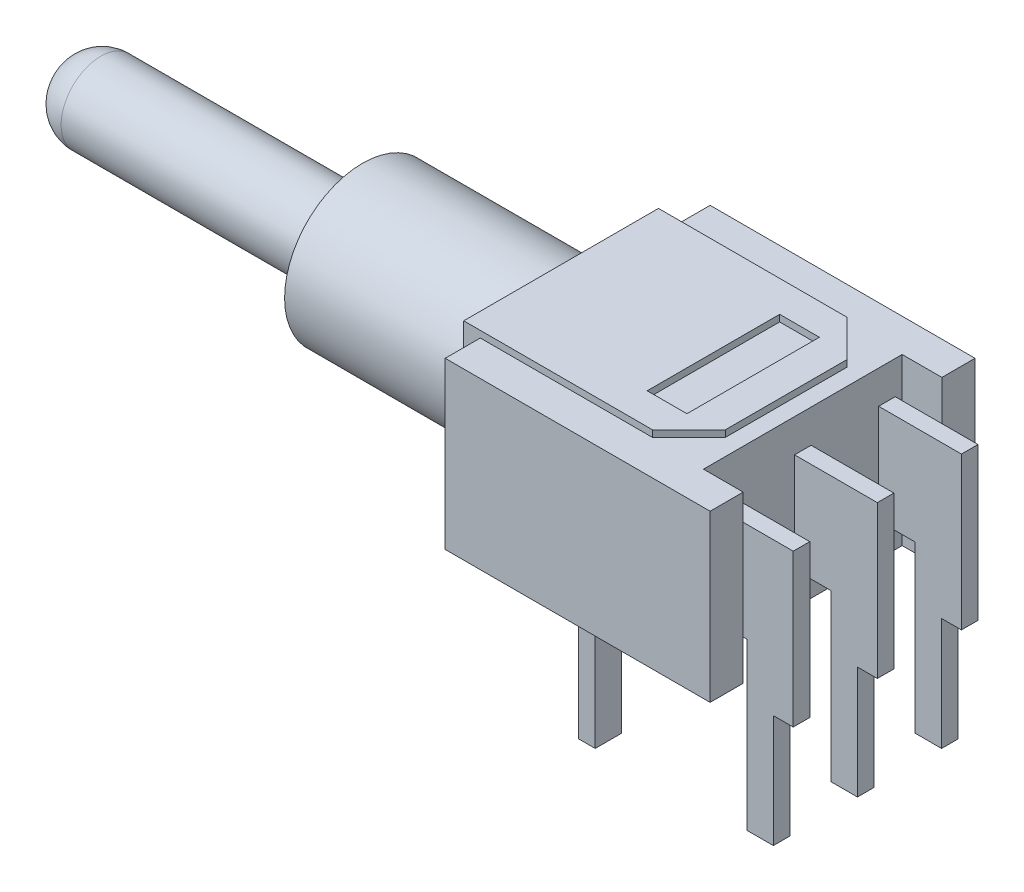
SolidWorks part; units mm, degrees
ref_plane "Plan de face" through (0, 0, 0) normal (0, 0, 1) x (1, 0, 0)
ref_plane "Plan de dessus" through (0, 0, 0) normal (0, 1, 0) x (1, 0, 0)
ref_plane "Plan de droite" through (0, 0, 0) normal (1, 0, 0) x (0, 0, -1)
sketch "Esquisse1" plane through (0, 0, 0) normal (0, 1, 0) x (1, 0, 0)
  line L0 (-0.5576, 4) -> (9.3741, 4) construction
  line L1 (0, 0) -> (8, 0)
  line L2 (0, 0) -> (0, 8)
  line L3 (0, 8) -> (8, 8)
  line L4 (8, 0) -> (8, 1)
  line L5 (9.3741, 7) -> (5.0476, 7) construction
  line L6 (6.8, -1.0514) -> (6.8, 8.7051) construction
  line L7 (8, 7) -> (6.8, 7)
  line L8 (8, 1) -> (6.8, 1)
  line L9 (6.8, 7) -> (6.8, 1)
  line L10 (8, 7) -> (8, 8)
  dimension "D1" = 4
  dimension "D2" = 1.2
  dimension "D3" = 1
extrude "Boss.-Extru.1" add sketch "Esquisse1" along normal blind 5
ref_plane "Plan1" through (0, 0, -4) normal (0, 0, 1) x (1, 0, 0)
sketch "Esquisse4" plane through (0, 0, -4) normal (0, 0, 1) x (1, 0, 0)
  line L0 (8, 5.6988) -> (8, 3.9014) construction
  line L1 (8, 5) -> (8, 0) construction
  line L2 (6.8, 5.6988) -> (6.8, -0.4202) construction
  line L3 (9.043, 5) -> (6.28, 5) construction
  line L4 (0, 5) -> (8, 5) construction
  line L5 (9.9987, 4) -> (6.28, 4) construction
  line L6 (9.3, 5.6988) -> (9.3, -4.6067) construction
  line L7 (7.9, 1.7201) -> (7.9, -5.9779) construction
  line L8 (7.1113, -4) -> (12.2122, -4) construction
  line L9 (6.28, 1) -> (8.5643, 1) construction
  line L10 (8.7, 0.5672) -> (8.7, -5.9778) construction
  line L11 (8.0742, 0) -> (11.7044, 0) construction
  line L12 (10.8115, -0.6) -> (8.3571, -0.6) construction
  line L13 (6.8, 4) -> (6.8, 1)
  line L14 (6.8, 1) -> (7.9, 1)
  line L15 (7.9, 1) -> (7.9, -4)
  line L16 (7.9, -4) -> (8.7, -4)
  line L17 (8.7, -4) -> (8.7, -0.6)
  line L18 (8.7, -0.6) -> (9.3, -0.6)
  line L19 (9.3, -0.6) -> (9.3, 4)
  line L20 (9.3, 4) -> (6.8, 4)
  dimension "D1" = 1.2
  dimension "D2" = 1
  dimension "D3" = 1.3
  dimension "D4" = 0.8
  dimension "D5" = 4
  dimension "D6" = 0.6
  dimension "D7" = 0.6
  dimension "D8" = 3
extrude "Boss.-Extru.2" add sketch "Esquisse4" along normal mid plane 0.5
sketch "Esquisse5" plane through (0, 0, -4) normal (0, 0, 1) x (1, 0, 0)
  line L0 (0, 5.5124) -> (0, -0.7298) construction
  line L1 (-0.5, 5.5124) -> (-0.5, -0.7298) construction
  line L2 (-0.7829, -0.5) -> (3.7936, -0.5) construction
  line L3 (3.47, -4.1096) -> (3.47, 0.4507) construction
  line L4 (2.97, -4.1096) -> (2.97, 0.6933) construction
  line L5 (7.6747, -4) -> (0.1874, -4) construction
  line L6 (-2.206, 5.2) -> (0.3815, 5.2) construction
  line L7 (8.3, -4.8535) -> (8.3, -2.7997) construction
  line L8 (3.22, -4.8535) -> (3.22, -2.5248) construction
  line L9 (0, 0) -> (8, 0) construction
  line L10 (0, 5) -> (8, 5) construction
  line L11 (0, 5.2) -> (0, 0)
  line L12 (0, 0) -> (2.77, 0)
  line L13 (3.47, -0.7) -> (3.47, -4)
  line L14 (3.47, -4) -> (2.97, -4)
  line L15 (2.97, -4) -> (2.97, -0.7)
  line L16 (2.77, -0.5) -> (-0.2, -0.5)
  line L17 (-0.5, -0.2) -> (-0.5, 5.2)
  line L18 (-0.5, 5.2) -> (0, 5.2)
  arc A0 (2.97, -0.7) -> (2.77, -0.5) centre (2.77, -0.7) ccw
  arc A1 (2.77, 0) -> (3.47, -0.7) centre (2.77, -0.7) cw
  arc A2 (-0.2, -0.5) -> (-0.5, -0.2) centre (-0.2, -0.2) cw
  point P35 (2.97, -0.5)
  point P38 (3.47, 0)
  point P41 (-0.5, -0.5)
  dimension "D7" = 0.2
  dimension "D8" = 0.7
  dimension "D9" = 0.3
  dimension "D1" = 0.25
  dimension "D2" = 0.5
  dimension "D3" = 5.08
  dimension "D4" = 0.5
  dimension "D5" = 0.5
  dimension "D6" = 0.2
extrude "Boss.-Extru.3" add sketch "Esquisse5" along normal mid plane 5.88
sketch "Esquisse6" plane through (3.47, 0, 0) normal (1, 0, 0) x (0, 0, -1)
  line L0 (8.4688, 0) -> (-0.8847, 0) construction
  line L1 (7.5, -4) -> (-1.0221, -4) construction
  line L2 (1.06, -4.4856) -> (1.06, 0.8968) construction
  line L3 (1.86, -4.4856) -> (1.86, 0.8968) construction
  line L4 (6.94, -4.4856) -> (6.94, 0.8968) construction
  line L5 (6.14, -4.4856) -> (6.14, 0.8968) construction
  line L7 (1.86, -4) -> (6.14, -4)
  line L8 (1.86, -4) -> (1.86, 0)
  line L9 (1.86, 0) -> (6.14, 0)
  line L10 (6.14, -4) -> (6.14, 0)
  dimension "D1" = 0.8
  dimension "D2" = 0.8
extrude "Enlèv. mat.-Extru.1" cut sketch "Esquisse6" against normal blind 0.7
sketch "Esquisse7" plane through (-0.5, 0, 0) normal (-1, 0, 0) x (0, 0, 1)
  line L0 (-6.94, -0.2) -> (-1.06, 5.2) construction
  line L1 (-1.06, 5.2) -> (-6.94, 5.2) construction
  line L2 (-1.06, 5.2) -> (-1.06, -0.2) construction
  line L3 (-6.94, 5.2) -> (-1.06, -0.2) construction
  line L4 (-1.06, -0.2) -> (-6.94, -0.2) construction
  circle A0 centre (-4, 2.5) radius 2.35
  circle A1 centre (-4, 2.5) radius 1.85
extrude "Boss.-Extru.4" add sketch "Esquisse7" along normal blind 6
sketch "Esquisse8" plane through (-0.5, 0, 0) normal (-1, 0, 0) x (0, 0, 1)
  circle A0 centre (-4, 2.5) radius 1.2
extrude "Boss.-Extru.5" add sketch "Esquisse8" along normal blind 15
fillet "Congé1" radius 1.1 1 edges at (-15.5, 1.3, -4)
sketch "Esquisse9" plane through (0, 5, 0) normal (0, 1, 0) x (1, 0, 0)
  line L0 (-1.2558, 6.94) -> (6.3347, 6.94) construction
  line L1 (-1.5452, 4) -> (12.278, 4) construction
  line L2 (6.3, 6.6378) -> (6.3, 0.8725) construction
  line L3 (5.2, 6.94) -> (7.0198, 5.1202) construction
  line L4 (5.2, 7.5949) -> (5.2, 5.3912) construction
  line L5 (4.1, 6.1625) -> (4.1, 3.2766) construction
  line L6 (5.3, 6.1625) -> (5.3, 3.0317) construction
  line L7 (2.8177, 6) -> (5.3, 6) construction
  line L9 (6.8, 1) -> (6.8, 7) construction
  line L10 (0, 6.94) -> (5.2, 6.94)
  line L11 (5.2, 6.94) -> (6.3, 5.84)
  line L12 (4.1, 6) -> (5.3, 6)
  line L13 (5.2, 1.06) -> (6.3, 2.16)
  line L14 (0, 1.06) -> (5.2, 1.06)
  line L15 (4.1, 2) -> (5.3, 2)
  line L16 (0, 6.94) -> (0, 1.06)
  line L17 (4.1, 6) -> (4.1, 2)
  line L18 (5.3, 6) -> (5.3, 2)
  line L19 (6.3, 5.84) -> (6.3, 2.16)
  dimension "D1" = 2.94
  dimension "D2" = 0.5
  dimension "D3" = 1.2
  dimension "D4" = 1
  dimension "D5" = 2
  dimension "D6" = 45
  dimension "D7" = 1.1
extrude "Boss.-Extru.6" add sketch "Esquisse9" along normal blind 0.2
pattern_linear "Répétition linéaire1" count 2 spacing 2.54 along (0, 0, -1) of "Boss.-Extru.2"
pattern_linear "Répétition linéaire2" count 2 spacing 2.54 along (0, 0, 1) of "Boss.-Extru.2"
